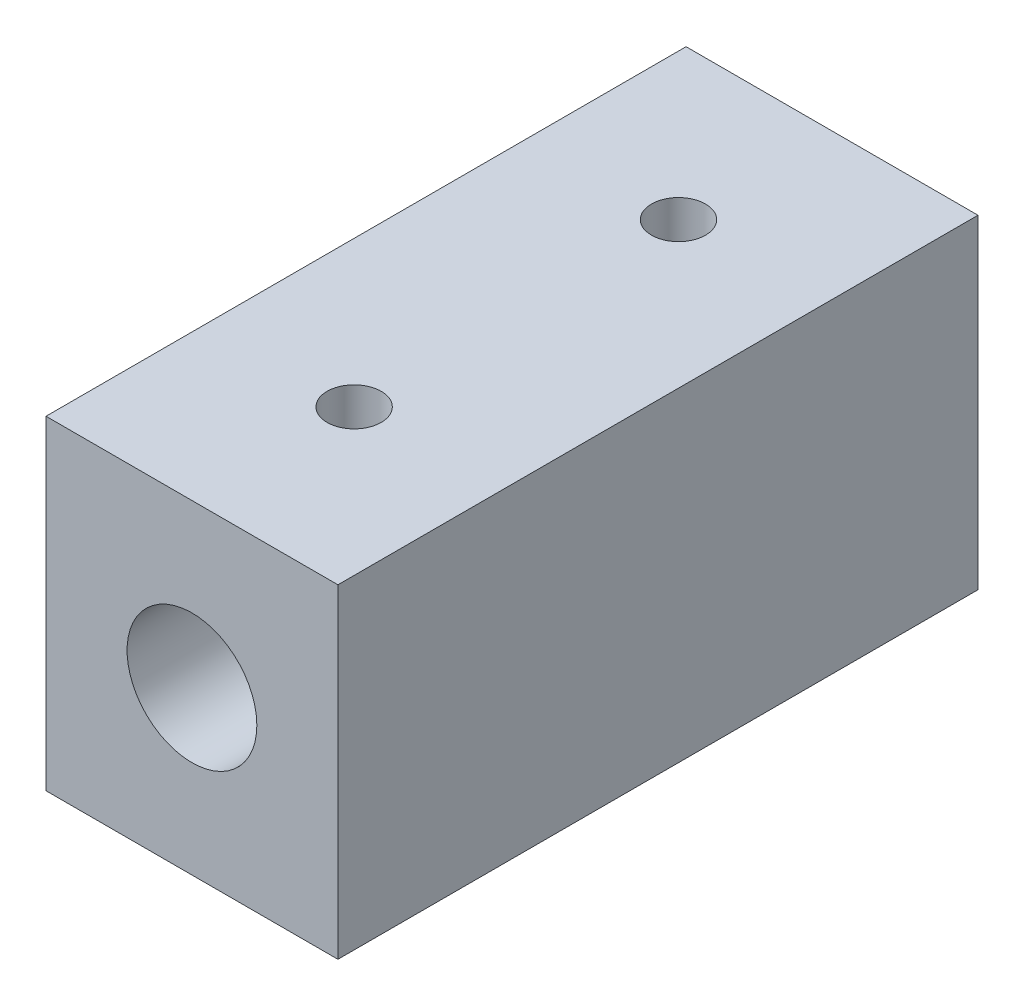
SolidWorks part; units mm, degrees
ref_plane "Front Plane" through (0, 0, 0) normal (0, 0, 1) x (1, 0, 0)
ref_plane "Top Plane" through (0, 0, 0) normal (0, 1, 0) x (1, 0, 0)
ref_plane "Right Plane" through (0, 0, 0) normal (1, 0, 0) x (0, 0, -1)
sketch "Sketch1" plane through (0, 0, 0) normal (0, 0, 1) x (1, 0, 0)
  line L0 (-6.75, 7.5) -> (6.75, 7.5)
  line L1 (-6.75, 7.5) -> (-6.75, -7.5)
  line L2 (6.75, 7.5) -> (6.75, -7.5)
  line L3 (-6.75, -7.5) -> (6.75, -7.5)
  line L4 (6.75, -7.5) -> (-6.75, 7.5) construction
  point P0 (0, 0)
  dimension "D1" = 13.5
  dimension "D2" = 15
extrude "Boss-Extrude1" add sketch "Sketch1" along normal mid plane 29.6
sketch "Sketch2" plane through (0, 0, 14.8) normal (0, 0, 1) x (1, 0, 0)
  circle A0 centre (0, 0) radius 3
  dimension "D1" = 6
extrude "Cut-Extrude1" cut sketch "Sketch2" against normal blind 28.8
sketch "Sketch3" plane through (0, 0, 14.8) normal (0, 0, 1) x (1, 0, 0)
  circle A0 centre (0, 0) radius 1.5
  dimension "D1" = 3
extrude "Cut-Extrude2" cut sketch "Sketch3" against normal through all
hole_wizard "M3x0.5 Tapped Hole1" positions "Sketch7" profile "Sketch8" tap size "M3x0.5" standard "ANSI Metric"
sketch "Sketch7" plane through (0, 7.5, 0) normal (0, 1, 0) x (1, 0, 0)
  line L0 (0, 7.7) -> (0, -7.3) construction
  line L2 (6.75, -14.8) -> (-6.75, -14.8) construction
  point P0 (0, 7.7)
  point P2 (0, -7.3)
  dimension "D1" = 7.5
  dimension "D2" = 15
sketch "Sketch8" plane through (0, 7.5, -7.7) normal (1, 0, 0) x (0, 0, 1)
  line L0 (0, 0) -> (0, 3.4511)
  line L1 (0, 3.4511) -> (1.25, 2.7)
  line L2 (1.25, 2.7) -> (1.25, 0)
  line L5 (1.25, 0) -> (0, 0)
  line L10 (0, 3.4511) -> (-1.25, 2.7) construction
  line L11 (0, -6.35) -> (0, 107.95) construction
  dimension "Tap Drill Dia." = 2.5
  dimension "Tap Drill Depth" = 2.7
  dimension "Drill Angle" = 118
cosmetic thread "Hole Thread1"
cosmetic thread "Hole Thread2"
